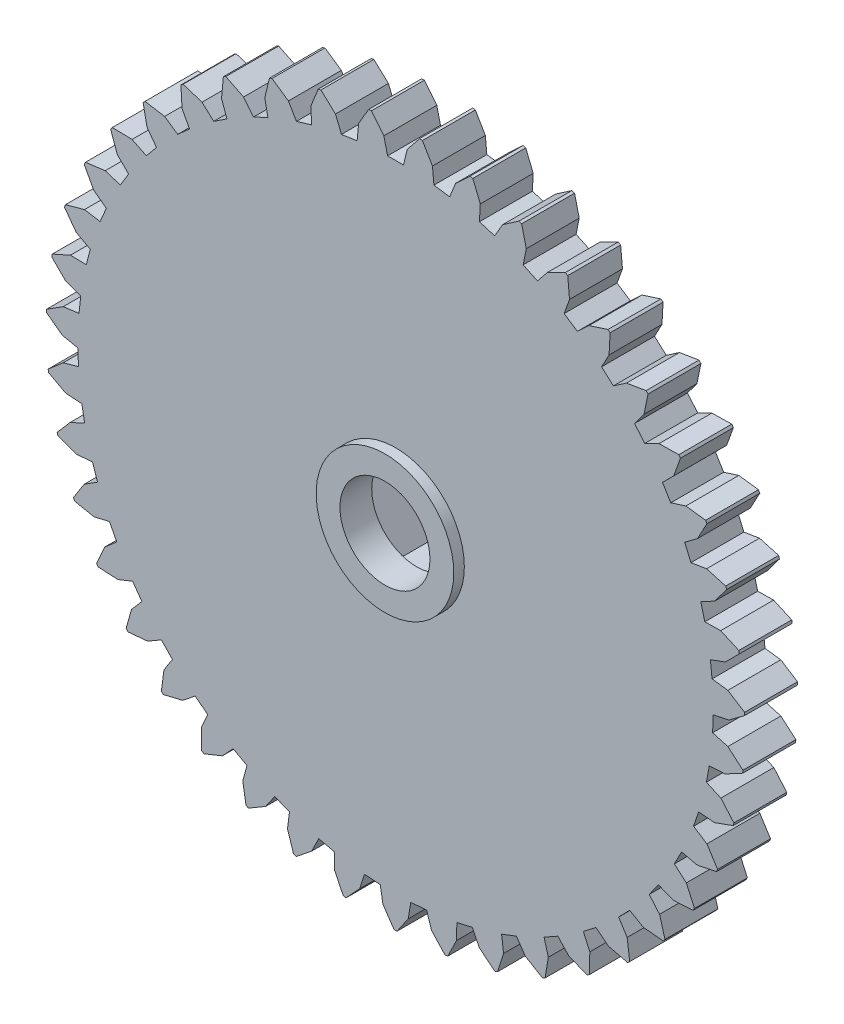
SolidWorks part; units mm, degrees
ref_plane "Plan de face" through (0, 0, 0) normal (0, 0, 1) x (1, 0, 0)
ref_plane "Plan de dessus" through (0, 0, 0) normal (0, 1, 0) x (1, 0, 0)
ref_plane "Plan de droite" through (0, 0, 0) normal (1, 0, 0) x (0, 0, -1)
sketch "Esquisse1" plane through (0, 0, 0) normal (0, 0, 1) x (1, 0, 0)
  circle A0 centre (0, 0) radius 33
  dimension "D1" = 66
extrude "Boss.-Extru.1" add sketch "Esquisse1" along normal blind 5
sketch "Esquisse2" plane through (0, 0, 0) normal (0, 0, -1) x (-1, 0, 0)
  line L0 (-2.2774, 32.9213) -> (-1.105, 31.4574)
  line L1 (-1.105, 31.4574) -> (-0.75, 30)
  line L2 (-0.75, 30) -> (0.75, 30)
  line L3 (0.75, 30) -> (1.105, 31.4574)
  line L4 (1.105, 31.4574) -> (2.2774, 32.9213)
  line L5 (-1.105, 31.4574) -> (1.105, 31.4574) construction
  line L6 (0, 33) -> (0, 30) construction
  circle A0 centre (0, 0) radius 33 construction
  arc A1 (-2.2774, 32.9213) -> (2.2774, 32.9213) centre (0, 0) cw
  dimension "D1" = 1.5
  dimension "D2" = 1.5
  dimension "D3" = 2.21
  dimension "D4" = 155
  dimension "D5" = 3
extrude "Enlèv. mat.-Extru.1" cut sketch "Esquisse2" against normal blind 6
pattern_circular "Répétition circulaire1" count 43 over 360 about axis through (0, 0, 0) along (0, 0, 1) of "Enlèv. mat.-Extru.1"
sketch "Esquisse3" plane through (0, 0, 0) normal (0, 0, -1) x (-1, 0, 0)
  circle A0 centre (0, 0) radius 10.5
  dimension "D1" = 21
extrude "Boss.-Extru.2" add sketch "Esquisse3" along normal blind 3
sketch "Esquisse4" plane through (0, 0, -3) normal (0, 0, -1) x (-1, 0, 0)
  line L1 (3.7528, -6.5) -> (7.5056, 0)
  line L2 (7.5056, 0) -> (3.7528, 6.5)
  line L3 (3.7528, 6.5) -> (-3.7528, 6.5)
  line L4 (-3.7528, 6.5) -> (-7.5056, 0)
  line L5 (-7.5056, 0) -> (-3.7528, -6.5)
  line L6 (-3.7528, -6.5) -> (3.7528, -6.5)
  circle A0 centre (0, 0) radius 6.5 construction
  dimension "D1" = 13
extrude "Enlèv. mat.-Extru.2" cut sketch "Esquisse4" against normal blind 6
sketch "Esquisse5" plane through (0, 0, 3) normal (0, 0, -1) x (-1, 0, 0)
  circle A0 centre (0, 0) radius 4.25
  dimension "D1" = 8.5
extrude "Enlèv. mat.-Extru.3" cut sketch "Esquisse5" against normal up to next
sketch "Esquisse6" plane through (0, 0, 0) normal (0, 0, -1) x (-1, 0, 0)
  circle A0 centre (0, 0) radius 33
  dimension "D1" = 66
sketch "Esquisse7" plane through (0, 0, 5) normal (0, 0, 1) x (1, 0, 0)
  circle A0 centre (0, 0) radius 6.5
  circle A1 centre (0, 0) radius 4.25
  dimension "D1" = 13
extrude "Boss.-Extru.3" add sketch "Esquisse7" along normal blind 1
